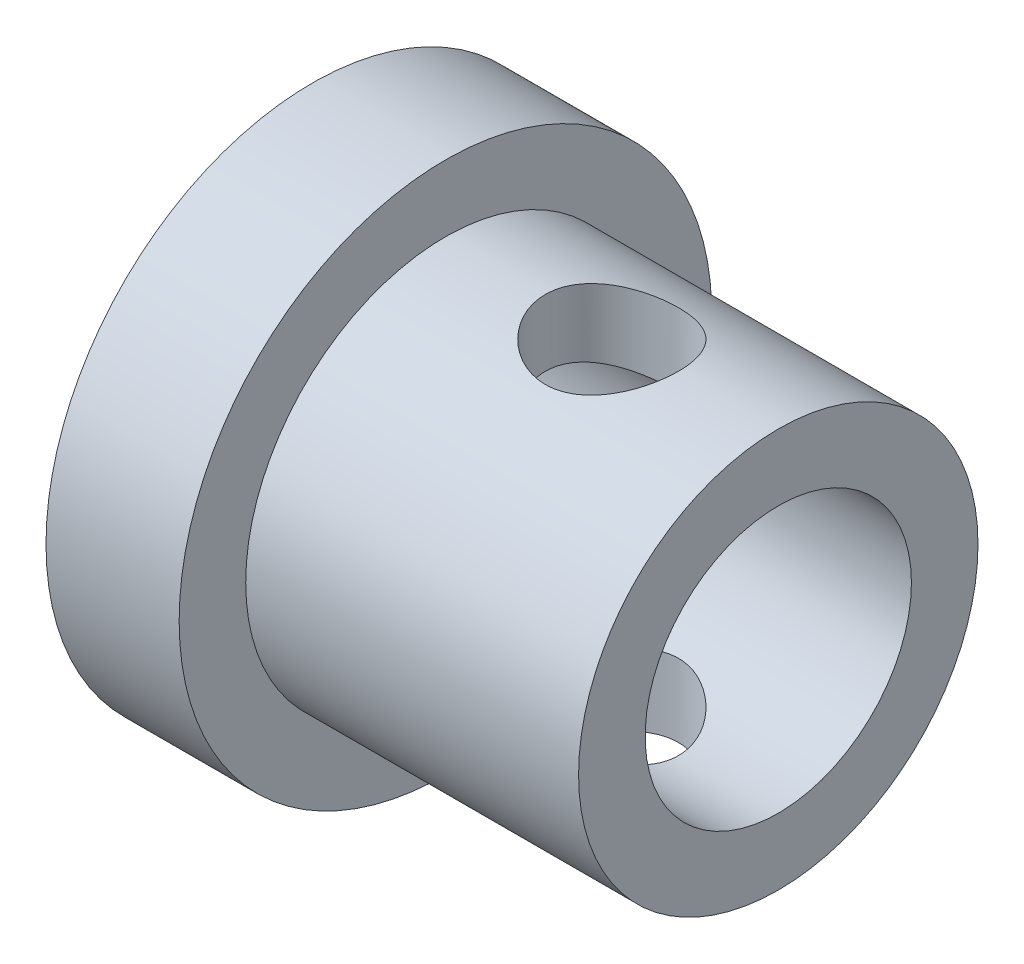
SolidWorks part; units mm, degrees
ref_plane "Front Plane" through (0, 0, 0) normal (0, 0, 1) x (1, 0, 0)
ref_plane "Top Plane" through (0, 0, 0) normal (0, 1, 0) x (1, 0, 0)
ref_plane "Right Plane" through (0, 0, 0) normal (1, 0, 0) x (0, 0, -1)
sketch "Sketch1" plane through (0, 0, 0) normal (1, 0, 0) x (0, 0, -1)
  circle A0 centre (0, 0) radius 3
  dimension "D1" = 6
extrude "Boss-Extrude1" add sketch "Sketch1" along normal mid plane 7
sketch "Sketch2" plane through (-3.5, 0, 0) normal (-1, 0, 0) x (0, 0, 1)
  circle A0 centre (0, 0) radius 4
  dimension "D1" = 8
extrude "Boss-Extrude2" add sketch "Sketch2" against normal blind 2
sketch "Sketch3" plane through (3.5, 0, 0) normal (1, 0, 0) x (0, 0, -1)
  circle A0 centre (0, 0) radius 2
  dimension "D1" = 4
extrude "Cut-Extrude1" cut sketch "Sketch3" against normal through all
sketch "Sketch4" plane through (0, 0, 0) normal (0, 1, 0) x (1, 0, 0)
  line L0 (3.5, -3) -> (3.5, 3) construction
  circle A0 centre (1, 0) radius 1
  dimension "D2" = 2
  dimension "D1" = 2.5
extrude "Cut-Extrude2" cut sketch "Sketch4" against normal through all both and the other way through all
